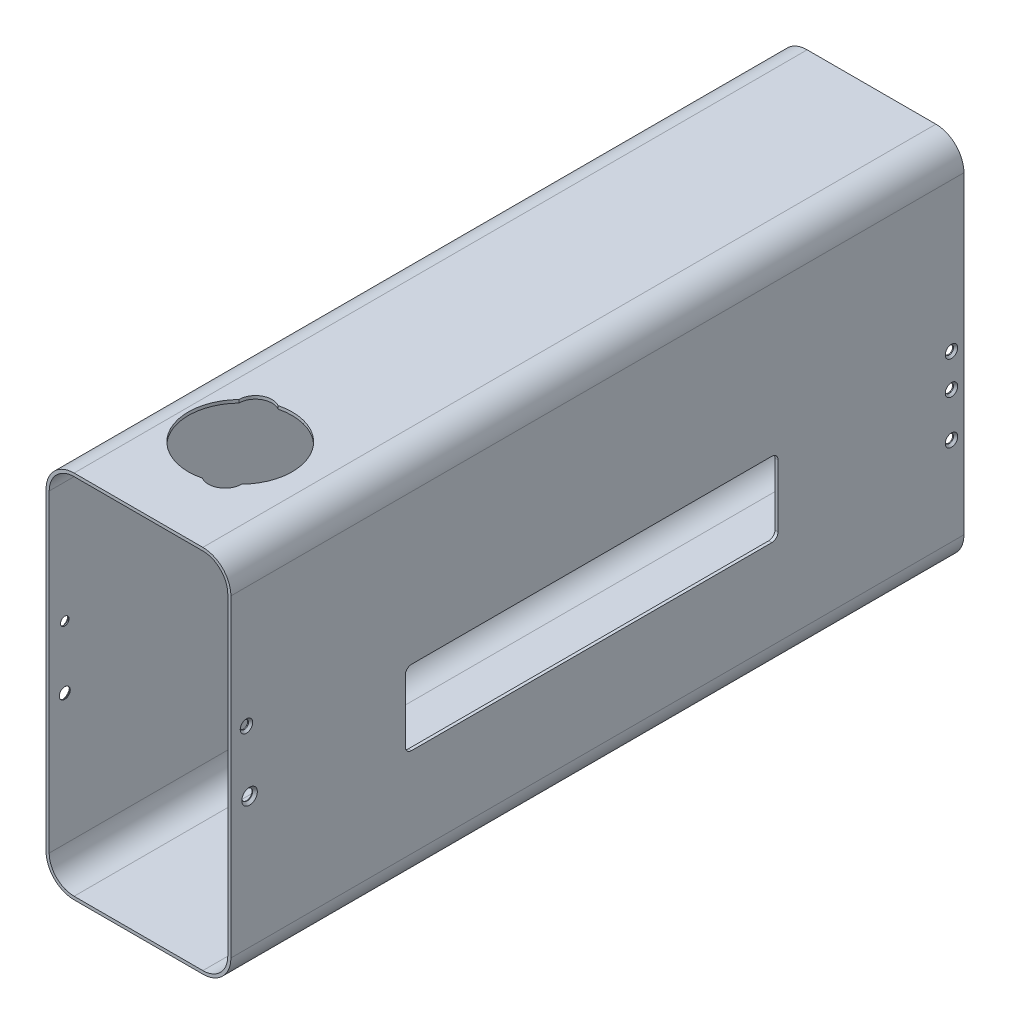
SolidWorks part; units mm, degrees
material "2024-T4"
ref_plane "Спереди" through (0, 0, 0) normal (0, 0, 1) x (1, 0, 0)
ref_plane "Сверху" through (0, 0, 0) normal (0, 1, 0) x (1, 0, 0)
ref_plane "Справа" through (0, 0, 0) normal (1, 0, 0) x (0, 0, -1)
sketch "Эскиз1" plane through (0, 0, 0) normal (0, 0, 1) x (1, 0, 0)
  line L0 (-44.5, -75.5) -> (-44.5, 75.5)
  line L1 (-31, -87.5) -> (31, -87.5)
  line L2 (-43, -75.5) -> (-43, 75.5)
  line L3 (-31, 87.5) -> (31, 87.5)
  line L4 (43, -75.5) -> (43, 75.5)
  line L5 (-43, -87.5) -> (43, 87.5) construction
  line L6 (-43, 87.5) -> (43, -87.5) construction
  line L7 (-31, 89) -> (31, 89)
  line L8 (44.5, -75.5) -> (44.5, 75.5)
  line L9 (-31, -89) -> (31, -89)
  arc A0 (-43, -75.5) -> (-31, -87.5) centre (-31, -75.5) ccw
  arc A1 (31, -87.5) -> (43, -75.5) centre (31, -75.5) ccw
  arc A2 (43, 75.5) -> (31, 87.5) centre (31, 75.5) ccw
  arc A3 (-31, 87.5) -> (-43, 75.5) centre (-31, 75.5) ccw
  arc A4 (-31, 89) -> (-44.5, 75.5) centre (-31, 75.5) ccw
  arc A5 (44.5, 75.5) -> (31, 89) centre (31, 75.5) ccw
  arc A6 (31, -89) -> (44.5, -75.5) centre (31, -75.5) ccw
  arc A7 (-44.5, -75.5) -> (-31, -89) centre (-31, -75.5) ccw
  point P0 (0, 0)
  dimension "D3" = 12
  dimension "D1" = 86
  dimension "D2" = 175
  dimension "D4" = 1.5
extrude "Бобышка-Вытянуть1" add sketch "Эскиз1" along normal blind 353
sketch "Эскиз2" plane through (44.5, 0, 0) normal (1, 0, 0) x (0, 0, -1)
  line L0 (-353, -75.5) -> (-353, 75.5) construction
  line L1 (-266, -32.5) -> (-92.5, -32.5)
  line L2 (-269, -29.5) -> (-269, 0.5)
  line L3 (-266, 3.5) -> (-92.5, 3.5)
  line L4 (-89.5, -29.5) -> (-89.5, 0.5)
  line L5 (-353, -89) -> (0, -89) construction
  arc A0 (-269, -29.5) -> (-266, -32.5) centre (-266, -29.5) ccw
  arc A1 (-92.5, -32.5) -> (-89.5, -29.5) centre (-92.5, -29.5) ccw
  arc A2 (-89.5, 0.5) -> (-92.5, 3.5) centre (-92.5, 0.5) ccw
  arc A3 (-266, 3.5) -> (-269, 0.5) centre (-266, 0.5) ccw
  dimension "D5" = 3
  dimension "D1" = 179.5
  dimension "D2" = 36
  dimension "D3" = 84
  dimension "D4" = 56.5
extrude "Вырез-Вытянуть1" cut sketch "Эскиз2" against normal up to next contours L3 A3 L2 A0 L1 A1 L4 A2
sketch "Эскиз3" plane through (0, 89, 0) normal (0, 1, 0) x (1, 0, 0)
  line L0 (31, 0) -> (-31, 0) construction
  line L1 (44.5, -353) -> (44.5, 0) construction
  line L2 (-2, -3.5) -> (-2, 0)
  line L3 (22, -3.5) -> (22, 0)
  arc A0 (-2, -3.5) -> (22, -3.5) centre (10, -3.5) ccw
  line M1 (31, 0) -> (-31, 0)
  dimension "D1" = 12
  dimension "D2" = 3.5
  dimension "D3" = 34.5
extrude "Вырез-Вытянуть2" [suppressed] cut sketch "Эскиз3" against normal up to next contours L2 A0 L3 M1
hole_wizard "M3_впотай_1" positions "Эскиз5" profile "Эскиз4" countersink size "M3" standard "DIN" end condition up to next
sketch "Эскиз5" plane through (44.5, 0, 0) normal (1, 0, 0) x (0, 0, -1)
  line L0 (-353, -87.5) -> (0, -87.5) construction
  line L1 (0, -75.5) -> (0, 75.5) construction
  line L2 (-353, -75.5) -> (-353, 75.5) construction
  line L3 (-353, -87.5) -> (0, -87.5) construction
  point P1 (-345.5, 17.5)
  point P13 (-6, 4)
  point P16 (-6, -12)
  point P19 (-6, -33)
  dimension "D1" = 16
  dimension "D2" = 21
  dimension "D3" = 105
  dimension "D7" = 54.5
  dimension "D8" = 6
  dimension "D9" = 7.5
sketch "Эскиз4" plane through (44.5, 17.5, 345.5) normal (0, 1, 0) x (0, 0, -1)
  line L0 (0, 0) -> (0, 1.5)
  line L1 (0, 1.5) -> (2.05, 1.5)
  line L2 (2, 1.45) -> (2, 1)
  line L3 (2, 1) -> (3, 0)
  line L5 (3, 0) -> (0, 0)
  line L6 (-2, 1) -> (-3, 0) construction
  line L7 (2.05, 1.5) -> (2, 1.45)
  line L8 (-2.05, 1.5) -> (-2, 1.45) construction
  line L11 (0, -6.35) -> (0, 107.95) construction
  dimension "Диаметр сквозного отверстия" = 4
  dimension "Глубина сквозного отверстия" = 1.5
  dimension "Диаметр передней зенковки" = 6
  dimension "Угол передней зенковки" = 90
  dimension "Диаметр задней зенковки" = 4.1
  dimension "Угол задней зенковки" = 90
hole_wizard "М3_впотай_2" positions "Эскиз7" profile "Эскиз6" countersink size "M3" standard "DIN" end condition up to next
sketch "Эскиз7" plane through (-44.5, 0, 0) normal (-1, 0, 0) x (0, 0, 1)
  line L1 (0, 75.5) -> (0, -75.5) construction
  line L3 (353, -87.5) -> (0, -87.5) construction
  circle A0 centre (345.5, 17.5) radius 2.05 construction
  point P1 (345.5, 17.5)
  point P14 (6, 3)
  point P17 (6, -33)
  point P21 (6, -18)
  dimension "D1" = 21
  dimension "D2" = 15
  dimension "D3" = 6
  dimension "D9" = 54.5
sketch "Эскиз6" plane through (-44.5, 17.5, 345.5) normal (0, 1, 0) x (0, 0, 1)
  line L0 (0, 0) -> (0, 1.5)
  line L1 (0, 1.5) -> (2.05, 1.5)
  line L2 (2, 1.45) -> (2, 1)
  line L3 (2, 1) -> (3, 0)
  line L5 (3, 0) -> (0, 0)
  line L6 (-2, 1) -> (-3, 0) construction
  line L7 (2.05, 1.5) -> (2, 1.45)
  line L8 (-2.05, 1.5) -> (-2, 1.45) construction
  line L11 (0, -6.35) -> (0, 107.95) construction
  dimension "Диаметр сквозного отверстия" = 4
  dimension "Глубина сквозного отверстия" = 1.5
  dimension "Диаметр передней зенковки" = 6
  dimension "Угол передней зенковки" = 90
  dimension "Диаметр задней зенковки" = 4.1
  dimension "Угол задней зенковки" = 90
sketch "Эскиз8" plane through (0, 89, 0) normal (0, 1, 0) x (1, 0, 0)
  line L0 (31, -353) -> (-31, -353) construction
  line L1 (-43, -353) -> (-43, 0) construction
  line L2 (6, -317.3205) -> (-14, -282.6795) construction
  line L3 (44.5, -353) -> (44.5, 0) construction
  arc A0 (-21.9999, -282.6506) -> (2.0251, -324.2631) centre (-4, -300) ccw
  arc A1 (2.0251, -324.2631) -> (13.9999, -317.3494) centre (6, -317.3205) ccw
  arc A2 (13.9999, -317.3494) -> (-10.0251, -275.7369) centre (-4, -300) ccw
  arc A3 (-21.9999, -282.6506) -> (-10.0251, -275.7369) centre (-14, -282.6795) cw
  dimension "D1" = 50
  dimension "D2" = 53
  dimension "D3" = 39
  dimension "D5" = 8
  dimension "D4" = 40
  dimension "D6" = 30
extrude "Вырез-Вытянуть3" cut sketch "Эскиз8" against normal up to next
hole_wizard "Зенковка для винта с потайной головкой M41" positions "Эскиз10" profile "Эскиз9" countersink size "M4" standard "DIN" end condition up to next
sketch "Эскиз10" plane through (44.5, 0, 0) normal (1, 0, 0) x (0, 0, -1)
  line L1 (-353, -75.5) -> (-353, 75.5) construction
  point P0 (-344, -12.5)
  dimension "D1" = 9
sketch "Эскиз9" plane through (44.5, -12.5, 344) normal (0, 1, 0) x (0, 0, -1)
  line L0 (0, 0) -> (0, 1.5)
  line L1 (0, 1.5) -> (2.65, 1.5)
  line L2 (2.6, 1.45) -> (2.6, 1.15)
  line L3 (2.6, 1.15) -> (3.75, 0)
  line L5 (3.75, 0) -> (0, 0)
  line L6 (-2.6, 1.15) -> (-3.75, 0) construction
  line L7 (2.65, 1.5) -> (2.6, 1.45)
  line L8 (-2.65, 1.5) -> (-2.6, 1.45) construction
  line L11 (0, -6.35) -> (0, 107.95) construction
  dimension "Диаметр сквозного отверстия" = 5.2
  dimension "Глубина сквозного отверстия" = 1.5
  dimension "Диаметр передней зенковки" = 7.5
  dimension "Угол передней зенковки" = 90
  dimension "Диаметр задней зенковки" = 5.3
  dimension "Угол задней зенковки" = 90
hole_wizard "Зенковка для винта с потайной головкой M43" positions "Эскиз14" profile "Эскиз13" countersink size "M4" standard "DIN" end condition up to next
sketch "Эскиз14" plane through (-44.5, 0, 0) normal (-1, 0, 0) x (0, 0, 1)
  point P0 (345.5, -12.5)
sketch "Эскиз13" plane through (-44.5, -12.5, 345.5) normal (0, 1, 0) x (0, 0, 1)
  line L0 (0, 0) -> (0, 1.5)
  line L1 (0, 1.5) -> (2.65, 1.5)
  line L2 (2.6, 1.45) -> (2.6, 1.15)
  line L3 (2.6, 1.15) -> (3.75, 0)
  line L5 (3.75, 0) -> (0, 0)
  line L6 (-2.6, 1.15) -> (-3.75, 0) construction
  line L7 (2.65, 1.5) -> (2.6, 1.45)
  line L8 (-2.65, 1.5) -> (-2.6, 1.45) construction
  line L11 (0, -6.35) -> (0, 107.95) construction
  dimension "Диаметр сквозного отверстия" = 5.2
  dimension "Глубина сквозного отверстия" = 1.5
  dimension "Диаметр передней зенковки" = 7.5
  dimension "Угол передней зенковки" = 90
  dimension "Диаметр задней зенковки" = 5.3
  dimension "Угол задней зенковки" = 90
